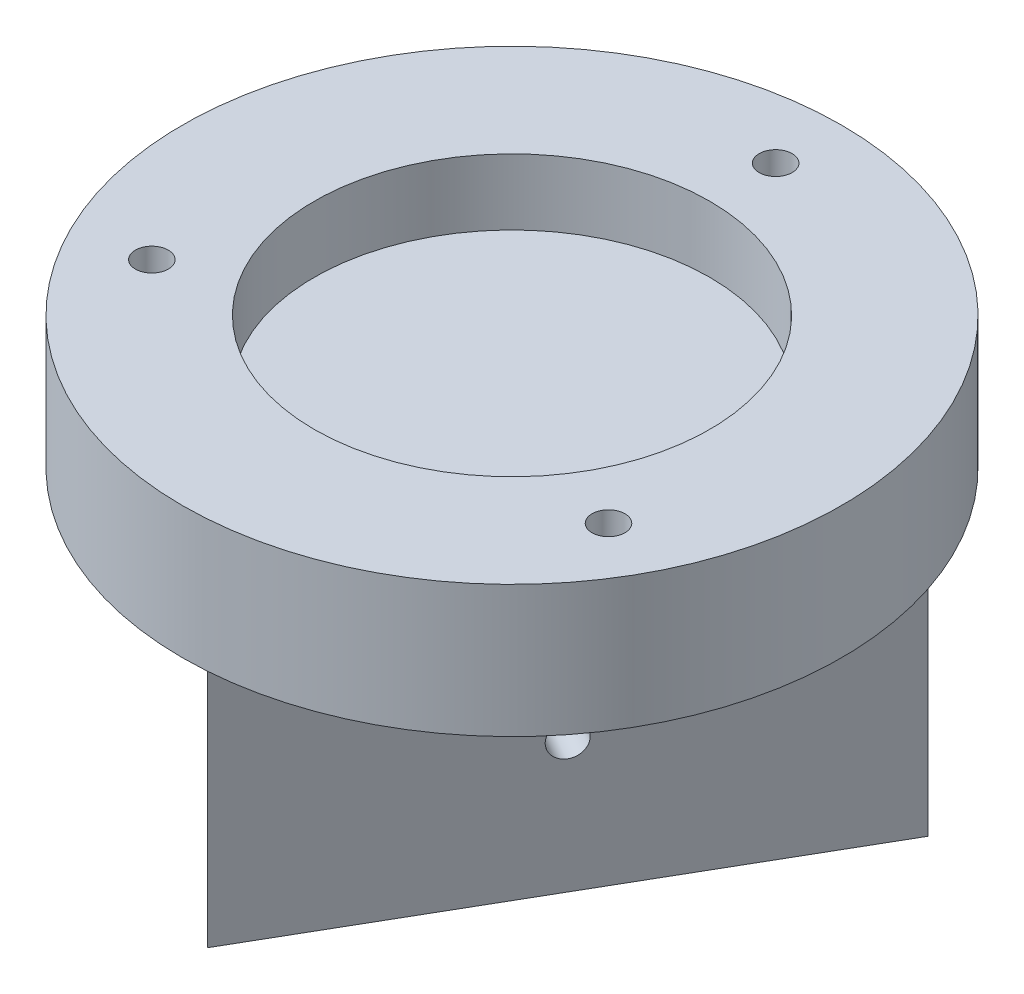
SolidWorks part; units mm, degrees
material "Polyetheretherketone (PEEK)"
ref_plane "Front Plane" through (0, 0, 0) normal (0, 0, 1) x (1, 0, 0)
ref_plane "Top Plane" through (0, 0, 0) normal (0, 1, 0) x (1, 0, 0)
ref_plane "Right Plane" through (0, 0, 0) normal (1, 0, 0) x (0, 0, -1)
sketch "Sketch1" plane through (0, 0, 0) normal (0, 1, 0) x (1, 0, 0)
  circle A0 centre (0, 0) radius 63.5
  dimension "RotatingDiskHousingOD" = 127
extrude "Boss-Extrude1" add sketch "Sketch1" along normal blind 25.4
sketch "Sketch2" plane through (0, 25.4, 0) normal (0, 1, 0) x (1, 0, 0)
  circle A0 centre (0, 0) radius 38.1
  dimension "RotatingDiskSeat" = 76.2
extrude "Cut-Extrude1" cut sketch "Sketch2" against normal blind 12.7
sketch "Sketch4" plane through (0, 0, 0) normal (0, -1, 0) x (1, 0, 0)
  line L0 (0, -1000) -> (0, 49000) construction
  line L1 (50.8, -29.3294) -> (0, 58.6588)
  line L2 (0, 58.6588) -> (-50.8, -29.3294)
  line L3 (-50.8, -29.3294) -> (50.8, -29.3294)
  circle A0 centre (0, 0) radius 29.3294 construction
  dimension "TriangleLegSeat" = 101.6
extrude "Boss-Extrude2" add sketch "Sketch4" along normal blind 50.8
sketch "Sketch5" plane through (0, 25.4, 0) normal (0, 1, 0) x (1, 0, 0)
  line L1 (0, 1.1179) -> (0, 43849.3163) construction
  line L3 (-50.8, 29.3294) -> (50.8, 29.3294) construction
  line L4 (-72.0003, -41.5694) -> (43229.2699, 24958.4306) construction
  line L5 (0, -58.6588) -> (-50.8, 29.3294) construction
  line L6 (-59.1352, 34.1417) -> (43242.135, -24965.8583) construction
  line L7 (50.8, 29.3294) -> (0, -58.6588) construction
  circle A0 centre (0, 0) radius 50.8 construction
  circle A1 centre (0, 50.8) radius 3.175
  circle A2 centre (43.9941, -25.4) radius 3.175
  circle A3 centre (-43.9941, -25.4) radius 3.175
  point P8 (0, 29.3294)
  point P14 (-25.4, -14.6647)
  point P19 (25.4, -14.6647)
  point P27 (0, 0)
  dimension "BoltCircleDiam" = 101.6
  dimension "BoltHoleDiam" = 6.35
  dimension "D1" = 3
extrude "Cut-Extrude2" cut sketch "Sketch5" against normal through all and the other way through all
sketch "Sketch6" plane through (25.4, 0, 14.6647) normal (0.866, 0, 0.5) x (0.5, 0, -0.866)
  line L0 (50.8, -50.8) -> (50.8, 0) construction
  line L1 (50.8, -50.8) -> (-50.8, -50.8) construction
  circle A0 centre (0, -25.4) radius 3.175
  dimension "D1" = 6.35
  dimension "D2" = 50.8
  dimension "D3" = 25.4
sketch "Sketch7" plane through (3.7546, 0, -29.3294) normal (0, 0, 1) x (1, 0, 0)
  line L2 (-54.5546, -50.8) -> (-54.5546, 0) construction
  line L3 (-54.5546, -50.8) -> (47.0454, -50.8) construction
  circle A0 centre (-3.7546, -25.4) radius 3.175
  dimension "D1" = 6.35
  dimension "D2" = 50.8
  dimension "D3" = 25.4
sketch "Sketch8" plane through (-25.4, 0, 14.6647) normal (-0.866, 0, 0.5) x (0.5, 0, 0.866)
  line L0 (50.8, -50.8) -> (-50.8, -50.8) construction
  line L1 (50.8, -50.8) -> (50.8, 0) construction
  circle A0 centre (0, -25.4) radius 3.175
  dimension "D1" = 6.35
  dimension "D2" = 25.4
  dimension "D3" = 50.8
extrude "Cut-Extrude3" cut sketch "Sketch8" against normal blind 15.24
extrude "Cut-Extrude5" cut sketch "Sketch7" along normal blind 15.24
extrude "Cut-Extrude6" cut sketch "Sketch6" against normal blind 15.24
equation "\"RotatingDiskHousingDiameter\"= (\"RotatingDiskDiam\" + 2)"
equation "\"ScopeLengthUnit\"= 10 * \"ScaleFactor\""
equation "\"EyepieceRadius\"= 0.75 * \"ScaleFactor\""
equation "\"ScopeThickness\"= 0.1 * \"ScaleFactor\""
equation "\"ScopeLensWidth\"= 2 * \"ScaleFactor\""
equation "\"ScopeOutsideRadius\"= 2.1 * \"ScaleFactor\""
equation "\"PegWidth\"=1"
equation "\"SupportOutsideDiam\"= \"ScopeOutsideRadius\" * 2 + .25"
equation "\"RotatingDiskDiam\"=3"
equation "\"RotatingDiskHousingOD@Sketch1\"=\"RotatingDiskHousingDiameter\""
equation "\"RotatingDiskSeat@Sketch2\" = \"RotatingDiskDiam\""
equation "\"LegSeatWidth\"=4 "
equation "\"TriangleLegSeat@Sketch4\"=\"LegSeatWidth\""
equation "\"LegSeatHeight\"=2"
equation "\"D1@Boss-Extrude2\"=\"LegSeatHeight\""
equation "\"BoltCircleDiam\"= ( \"RotatingDiskDiam\" + \"RotatingDiskHousingDiameter\" ) / 2"
equation "\"BoltCircleDiam@Sketch5\"=\"BoltCircleDiam\""
equation "\"D2@Sketch6\"=\"LegSeatWidth\"/2"
equation "\"D3@Sketch6\"=\"LegSeatHeight\"/2"
equation "\"D2@Sketch7\"=\"LegSeatWidth\"/2"
equation "\"D3@Sketch7\"=\"LegSeatHeight\"/2"
equation "\"D2@Sketch8\"=\"LegSeatHeight\"/2"
equation "\"D3@Sketch8\"=\"LegSeatWidth\"/2"
equation "\"LegThickness\"=0.25"
equation "\"LegHeight\"=48"
equation "\"LegBoltDiam\"=0.25"
equation "\"PinHeight\"=\"RotDiskLidHeight\" + \"RotDiskHeight\" + \"PinBoltDiam\"*3"
equation "\"PinBoltDiam\"=0.25"
equation "\"RotDiskHeight\"=0.5"
equation "\"RotDiskLidHeight\"= 0.5"
equation "\"DiskSeatPinDiam\"=0.25"
equation "\"BoltHoleDiam@Sketch5\"=\"DiskSeatPinDiam\""
equation "\"D1@Cut-Extrude1\"=\"RotDiskHeight\""
equation "\"ScaleFactor\"= 1"
